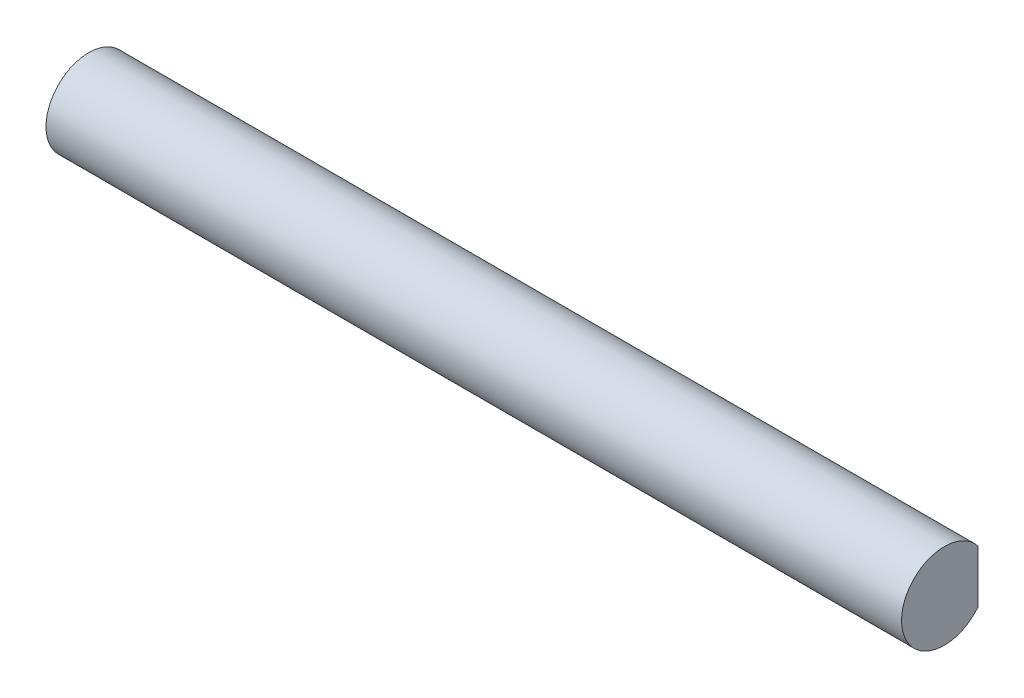
SolidWorks part; units mm, degrees
ref_plane "Front Plane" through (0, 0, 0) normal (0, 0, 1) x (1, 0, 0)
ref_plane "Top Plane" through (0, 0, 0) normal (0, 1, 0) x (1, 0, 0)
ref_plane "Right Plane" through (0, 0, 0) normal (1, 0, 0) x (0, 0, -1)
sketch "Sketch1" plane through (0, 0, 0) normal (1, 0, 0) x (0, 0, -1)
  line L0 (2.3617, 1.85) -> (2.3617, -1.85)
  arc A0 (2.3617, 1.85) -> (2.3617, -1.85) centre (0, 0) ccw
  dimension "D1" = 6
  dimension "D2" = 3.7
extrude "Boss-Extrude1" add sketch "Sketch1" along normal blind 60
